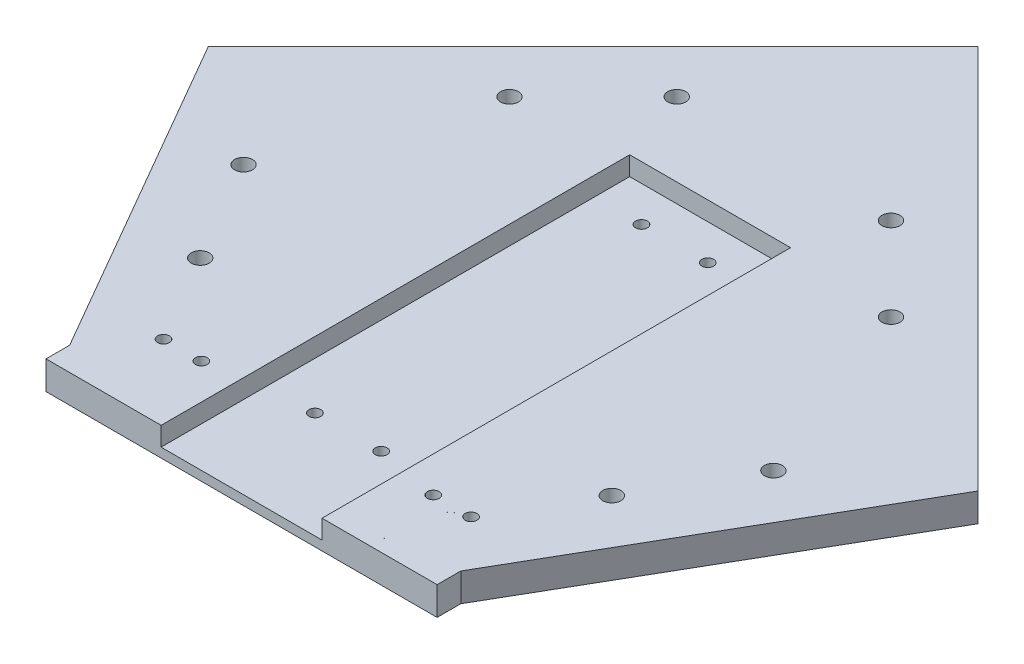
SolidWorks part; units mm, degrees
ref_plane "Front Plane" through (0, 0, 0) normal (0, 0, 1) x (1, 0, 0)
ref_plane "Top Plane" through (0, 0, 0) normal (0, 1, 0) x (1, 0, 0)
ref_plane "Right Plane" through (0, 0, 0) normal (1, 0, 0) x (0, 0, -1)
sketch "Sketch1" plane through (0, 0, 0) normal (0, 1, 0) x (1, 0, 0)
  line L0 (0, 66.2201) -> (-81.3173, -15.0971)
  line L1 (0, 66.2201) -> (81.3173, -15.0971)
  line L2 (-81.3173, -15.0971) -> (-41.3173, -84.3792)
  line L3 (81.3173, -15.0971) -> (41.3173, -84.3792)
  line L4 (-41.3173, -84.3792) -> (-41.3173, -89.3792)
  line L5 (41.3173, -84.3792) -> (41.3173, -89.3792)
  line L6 (-41.3173, -89.3792) -> (41.3173, -89.3792)
extrude "Boss-Extrude1" add sketch "Sketch1" along normal blind 6 contours L4 L6 L5 L3 L1 L0 L2
sketch "Sketch2" plane through (0, 6, 0) normal (0, 1, 0) x (1, 0, 0)
  line L0 (-41.3173, -89.3792) -> (41.3173, -89.3792) construction
  line L1 (-16.9977, -89.3792) -> (17.0023, -89.3792)
  line L2 (-16.9977, -89.3792) -> (-16.9977, 9.6208)
  line L3 (-16.9977, 9.6208) -> (17.0023, 9.6208)
  line L4 (17.0023, -89.3792) -> (17.0023, 9.6208)
  dimension "D1" = 34
  dimension "D2" = 99
  dimension "D3" = 24.315
extrude "Cut-Extrude1" cut sketch "Sketch2" against normal blind 4
sketch "Sketch3" plane through (0, 6, 0) normal (0, 1, 0) x (1, 0, 0)
  line L0 (-40.6586, 25.5615) -> (0, -15.0971) construction
  line L1 (0, 66.2201) -> (-81.3173, -15.0971) construction
  line L2 (0, -15.0971) -> (40.6586, 25.5615) construction
  line L3 (0, 66.2201) -> (81.3173, -15.0971) construction
  line L4 (0, -15.0971) -> (60.988, -50.3086) construction
  line L6 (81.3173, -15.0971) -> (41.3173, -84.3792) construction
  line L8 (0, -15.0971) -> (-60.988, -50.3086) construction
  line L9 (-81.3173, -15.0971) -> (-41.3173, -84.3792) construction
  dimension "D1" = 90
sketch "Sketch4" plane through (0, 6, 0) normal (0, 1, 0) x (1, 0, 0)
  line L0 (0, 66.2201) -> (-81.3173, -15.0971) construction
  line L1 (-40.6586, 25.5615) -> (0, -15.0971) construction
  line L2 (-81.3173, -15.0971) -> (-41.3173, -84.3792) construction
  line L3 (0, -15.0971) -> (-60.988, -50.3086) construction
  line L4 (81.3173, -15.0971) -> (41.3173, -84.3792) construction
  line L5 (0, -15.0971) -> (60.988, -50.3086) construction
  line L6 (0, 66.2201) -> (81.3173, -15.0971) construction
  line L7 (0, -15.0971) -> (40.6586, 25.5615) construction
  circle A0 centre (-22.6274, 25.2079) radius 1.9
  circle A1 centre (-40.3051, 7.5303) radius 1.9
  circle A2 centre (-55.9796, -32.9832) radius 1.9
  circle A3 centre (-43.4796, -54.6339) radius 1.9
  circle A4 centre (43.4796, -54.6339) radius 1.9
  circle A5 centre (55.9796, -32.9832) radius 1.9
  circle A6 centre (22.6274, 25.2079) radius 1.9
  circle A7 centre (40.3051, 7.5303) radius 1.9
  dimension "D1" = 13
  dimension "D2" = 13
  dimension "D3" = 12.5
  dimension "D4" = 12.5
  dimension "D5" = 13
  dimension "D6" = 13
  dimension "D7" = 12.5
  dimension "D8" = 12.5
  dimension "D9" = 13
  dimension "D10" = 13
  dimension "D11" = 12.5
  dimension "D12" = 12.5
  dimension "D13" = 13
  dimension "D14" = 13
  dimension "D15" = 12.5
  dimension "D16" = 12.5
extrude "Cut-Extrude2" cut sketch "Sketch4" against normal through all
sketch "Sketch5" plane through (0, 6, 0) normal (0, 1, 0) x (1, 0, 0)
  line L0 (-41.3173, -89.3792) -> (-16.9977, -89.3792) construction
  line L1 (17.0023, -89.3792) -> (41.3173, -89.3792) construction
  line L2 (17.0023, -89.3792) -> (17.0023, 9.6208) construction
  line L3 (-16.9977, 9.6208) -> (-16.9977, -89.3792) construction
  line L4 (17.0023, -89.3792) -> (17.0023, 9.6208) construction
  circle A0 centre (-28.4977, -73.3792) radius 1.8
  circle A1 centre (28.5023, -73.3792) radius 1.8
  circle A2 centre (26.0023, -86.3792) radius 1.25
  circle A3 centre (-25.9977, -86.3792) radius 1.25
  dimension "D1" = 16
  dimension "D5" = 9
  dimension "D2" = 16
  dimension "D3" = 11.5
  dimension "D4" = 11.5
  dimension "D6" = 3
  dimension "D7" = 9
  dimension "D8" = 3
extrude "Cut-Extrude3" cut sketch "Sketch5" against normal blind 10
sketch "Sketch6" plane through (0, 2, 0) normal (0, 1, 0) x (1, 0, 0)
  line L0 (17.0023, 9.6208) -> (-16.9977, 9.6208) construction
  line L1 (-16.9977, -89.3792) -> (17.0023, -89.3792) construction
  circle A0 centre (7.0023, 2.1208) radius 1.25
  circle A1 centre (-6.9977, 2.1208) radius 1.25
  circle A2 centre (-6.9977, -66.8792) radius 1.25
  circle A3 centre (7.0023, -66.8792) radius 1.25
  point P6 (0.0023, 9.6208)
  point P7 (0.0023, 9.6208)
  dimension "D1" = 7.5
  dimension "D5" = 22.5
  dimension "D2" = 7.5
  dimension "D3" = 7
  dimension "D4" = 7
  dimension "D6" = 22.5
extrude "Cut-Extrude4" cut sketch "Sketch6" against normal blind 10
sketch "Sketch7" plane through (0, 6, 0) normal (0, 1, 0) x (1, 0, 0)
  circle A0 centre (-32.4977, -73.3792) radius 1.25
  circle A1 centre (-24.4977, -73.3792) radius 1.25
  circle A2 centre (-28.4977, -73.3792) radius 1.8 construction
  dimension "D1" = 2.5
  dimension "D2" = 4
  dimension "D3" = 4
extrude "Cut-Extrude5" cut sketch "Sketch7" against normal blind 10
mirror "Mirror1" about plane through (0, 0, 0) normal (1, 0, 0) of "Cut-Extrude5"
sketch "Sketch8" plane through (0, 6, 0) normal (0, 1, 0) x (1, 0, 0)
  circle A0 centre (-28.4977, -73.3792) radius 1.8
  circle A2 centre (-25.9977, -86.3792) radius 1.25
extrude "Boss-Extrude2" add sketch "Sketch8" against normal blind 6
mirror "Mirror2" about plane through (0, 0, 0) normal (1, 0, 0) of "Boss-Extrude2"
